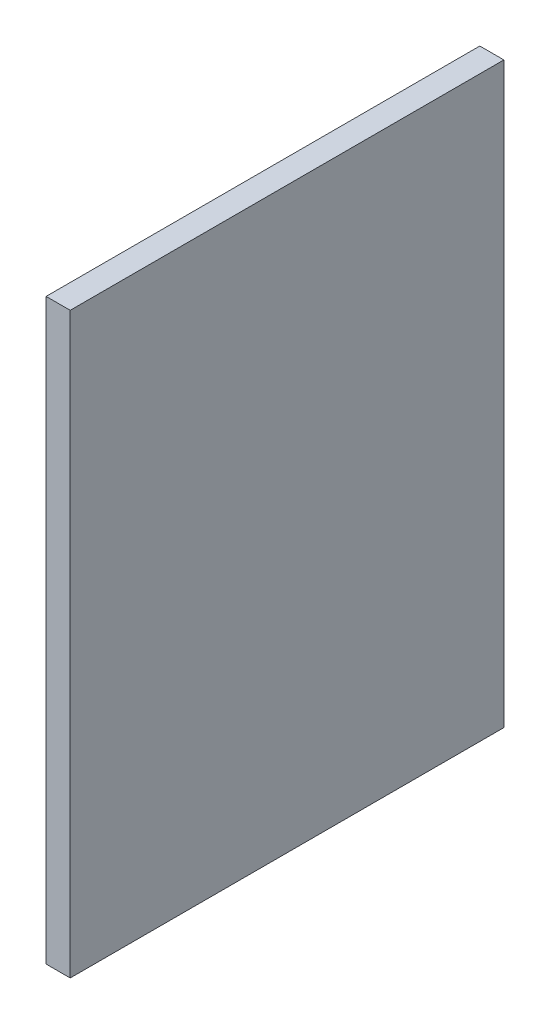
SolidWorks part; units mm, degrees
material "ASTM A36 Steel"
ref_plane "Front Plane" through (0, 0, 0) normal (0, 0, 1) x (1, 0, 0)
ref_plane "Top Plane" through (0, 0, 0) normal (0, 1, 0) x (1, 0, 0)
ref_plane "Right Plane" through (0, 0, 0) normal (1, 0, 0) x (0, 0, -1)
sketch "Sketch1" plane through (0, 0, 0) normal (1, 0, 0) x (0, 0, -1)
  line L1 (28.575, 38.1) -> (-28.575, 38.1)
  line L2 (28.575, 38.1) -> (28.575, -38.1)
  line L3 (28.575, -38.1) -> (-28.575, -38.1)
  line L4 (-28.575, 38.1) -> (-28.575, -38.1)
  line L5 (28.575, 38.1) -> (-28.575, -38.1) construction
  line L6 (28.575, -38.1) -> (-28.575, 38.1) construction
  point P0 (0, 0)
  dimension "D1" = 76.2
  dimension "D2" = 57.15
extrude "Boss-Extrude1" add sketch "Sketch1" along normal mid plane 3.175
